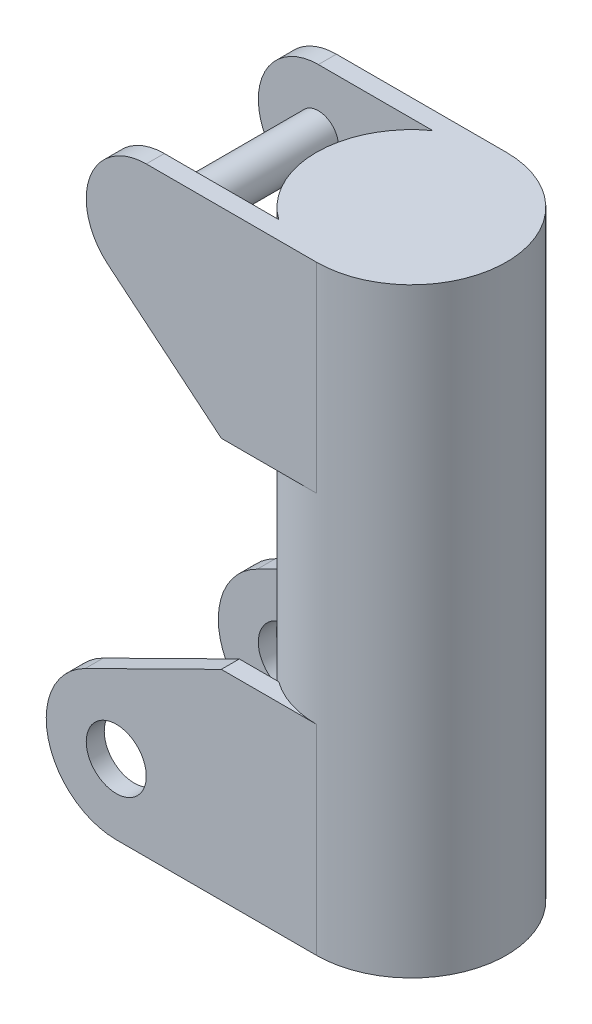
SolidWorks part; units mm, degrees
material "AISI 4340 Steel, normalized"
ref_plane "Front Plane" through (0, 0, 0) normal (0, 0, 1) x (1, 0, 0)
ref_plane "Top Plane" through (0, 0, 0) normal (0, 1, 0) x (1, 0, 0)
ref_plane "Right Plane" through (0, 0, 0) normal (1, 0, 0) x (0, 0, -1)
sketch "Sketch1" plane through (0, 0, 0) normal (0, 1, 0) x (1, 0, 0)
  circle A0 centre (0, 0) radius 95
  dimension "D1" = 190
extrude "Boss-Extrude1" add sketch "Sketch1" along normal blind 600
shell "Shell1" thickness 10
ref_plane "Plane1" through (0, 0, -95) normal (0, 0, -1) x (-1, 0, 0)
sketch "Sketch2" plane through (0, 0, -95) normal (0, 0, -1) x (-1, 0, 0)
  line L0 (0, 0) -> (95, 0)
  line L1 (-95, 0) -> (95, 0) construction
  line L2 (95, 0) -> (200, 0)
  line L3 (231.0236, 132.7498) -> (95, 200)
  line L4 (95, 0) -> (95, 600) construction
  line L5 (95, 200) -> (0, 200)
  line L6 (0, 200) -> (0, 0)
  line L7 (0, 600) -> (95, 600)
  line L8 (95, 600) -> (-95, 600) construction
  line L9 (95, 600) -> (170, 600)
  line L10 (208.2659, 493.7861) -> (95, 400)
  line L11 (95, 400) -> (0, 400)
  line L12 (0, 400) -> (0, 600)
  arc A0 (200, 0) -> (231.0236, 132.7498) centre (200, 70) ccw
  circle A1 centre (200, 70) radius 30
  arc A2 (208.2659, 493.7861) -> (170, 600) centre (170, 540) ccw
  circle A3 centre (170, 540) radius 20 construction
  point P22 (150.8676, 439.1983)
  dimension "D1" = 60
  dimension "D2" = 40
  dimension "D5" = 40
  dimension "D6" = 40
  dimension "D3" = 200
  dimension "D4" = 200
  dimension "D7" = 200
  dimension "D8" = 170
extrude "Boss-Extrude2" add sketch "Sketch2" against normal blind 18
sketch "Sketch3" plane through (0, 600, 0) normal (0, 1, 0) x (1, 0, 0)
  line L0 (-95, 0) -> (95, 0) construction
  arc A0 (-55.6417, 77) -> (0, 95) centre (0, 0) ccw construction
ref_plane "Plane2" through (0, 0, 0) normal (0, 0, -1) x (-1, 0, 0)
mirror "Mirror1" about plane through (0, 0, 0) normal (0, 0, -1) of "Boss-Extrude2"
sketch "Sketch4" plane through (0, 0, 0) normal (0, 0, 1) x (1, 0, 0)
  circle A0 centre (-170, 540) radius 20 construction
  circle A1 centre (-170, 540) radius 20
extrude "Boss-Extrude3" add sketch "Sketch4" along normal mid plane 190
